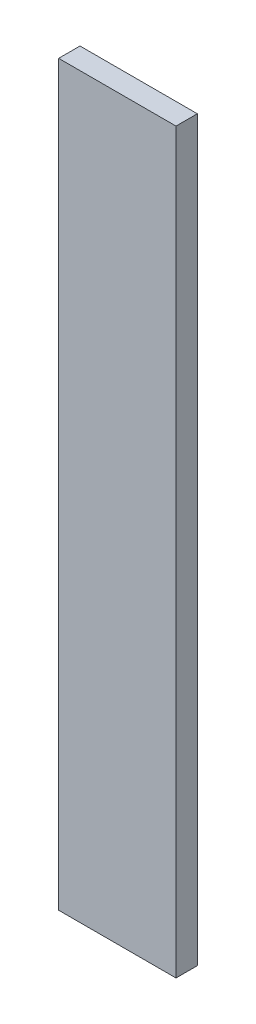
SolidWorks part; units mm, degrees
ref_plane "Front Plane" through (0, 0, 0) normal (0, 0, 1) x (1, 0, 0)
ref_plane "Top Plane" through (0, 0, 0) normal (0, 1, 0) x (1, 0, 0)
ref_plane "Right Plane" through (0, 0, 0) normal (1, 0, 0) x (0, 0, -1)
sketch "Sketch1" plane through (0, 0, 0) normal (0, 0, 1) x (1, 0, 0)
  line L0 (23, 395) -> (23, 0) construction
  line L1 (-23, 0) -> (43, 0)
  line L2 (-23, 0) -> (-23, 415)
  line L3 (-23, 415) -> (43, 415)
  line L4 (43, 0) -> (43, 415)
  line L5 (-23, 395) -> (23, 395) construction
  line L7 (23, 395) -> (-23, 395)
  line L8 (23, 395) -> (23, 0)
  line L9 (23, 0) -> (-23, 0)
  line L10 (-23, 395) -> (-23, 0)
  point P9 (0, 395)
  dimension "D1" = 20
  dimension "D2" = 20
extrude "Boss-Extrude1" add sketch "Sketch1" against normal blind 6 contours L7 L8 L1 L4 L3 L2
sketch "Sketch2" plane through (0, 0, 0) normal (0, 0, 1) x (1, 0, 0)
  line L1 (43, 415) -> (-23, 415)
  line L2 (43, 415) -> (43, 0)
  line L3 (43, 0) -> (-23, 0)
  line L4 (-23, 415) -> (-23, 0)
extrude "Boss-Extrude2" add sketch "Sketch2" along normal blind 6
sketch "Sketch3" plane through (0, 0, -6) normal (0, 0, -1) x (-1, 0, 0)
  circle A0 centre (-23, 395) radius 10
  dimension "D1" = 20
extrude "Cut-Extrude1" cut sketch "Sketch3" against normal up to surface (6 mm away) up to face at (0, 197.5, 0)
